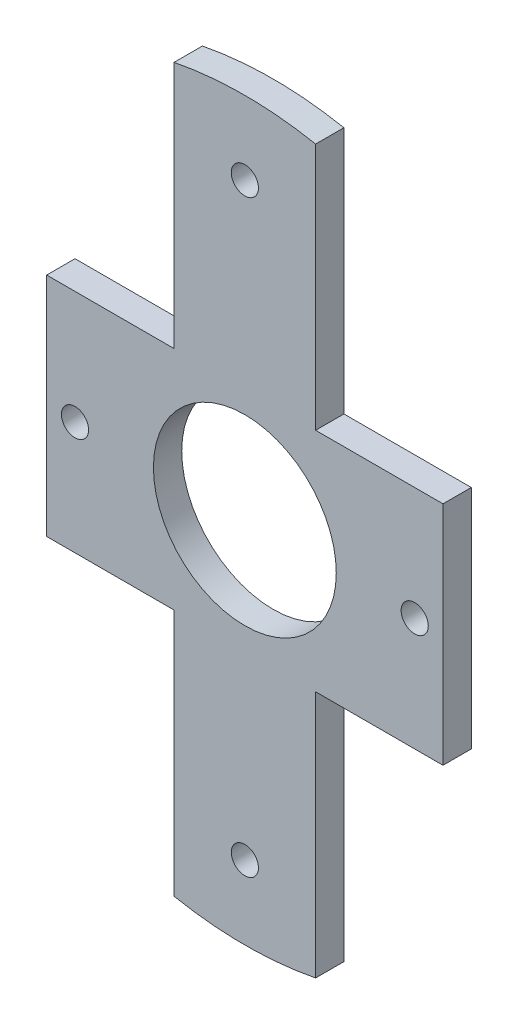
SolidWorks part; units mm, degrees
ref_plane "Front Plane" through (0, 0, 0) normal (0, 0, 1) x (1, 0, 0)
ref_plane "Top Plane" through (0, 0, 0) normal (0, 1, 0) x (1, 0, 0)
ref_plane "Right Plane" through (0, 0, 0) normal (1, 0, 0) x (0, 0, -1)
sketch "Sketch1" plane through (0, 0, 0) normal (0, 0, 1) x (1, 0, 0)
  line L0 (0, 0) -> (0, 65) construction
  line L1 (0, 0) -> (65, 0) construction
  line L2 (12.5, 20) -> (35, 20)
  line L3 (35, 20) -> (35, 0)
  line L4 (12.5, 20) -> (12.5, 63.7868)
  line L5 (-35, 20) -> (-35, -20)
  line L6 (-12.5, 20) -> (-35, 20)
  line L7 (-12.5, 20) -> (-12.5, 63.7868)
  line L8 (12.5, -20) -> (35, -20)
  line L9 (12.5, -20) -> (12.5, -63.7868)
  line L10 (-12.5, -20) -> (-12.5, -63.7868)
  line L11 (-12.5, -20) -> (-35, -20)
  line L12 (35, -20) -> (35, 0)
  arc A0 (-12.5, -63.7868) -> (12.5, -63.7868) centre (0, 0) ccw
  circle A1 centre (0, 0) radius 16.15
  arc A2 (12.5, 63.7868) -> (-12.5, 63.7868) centre (0, 0) ccw
  circle A3 centre (0, 52) radius 2.4
  circle A4 centre (30, 0) radius 2.4
  circle A5 centre (0, -52) radius 2.4
  circle A6 centre (-30, 0) radius 2.4
  point P20 (-35, 0)
  dimension "D1" = 130
  dimension "D2" = 32.3
  dimension "D6" = 4.8
  dimension "D8" = 4.8
  dimension "D3" = 20
  dimension "D4" = 70
  dimension "D5" = 25
  dimension "D7" = 52
  dimension "D9" = 30
extrude "Boss-Extrude1" add sketch "Sketch1" along normal blind 5
